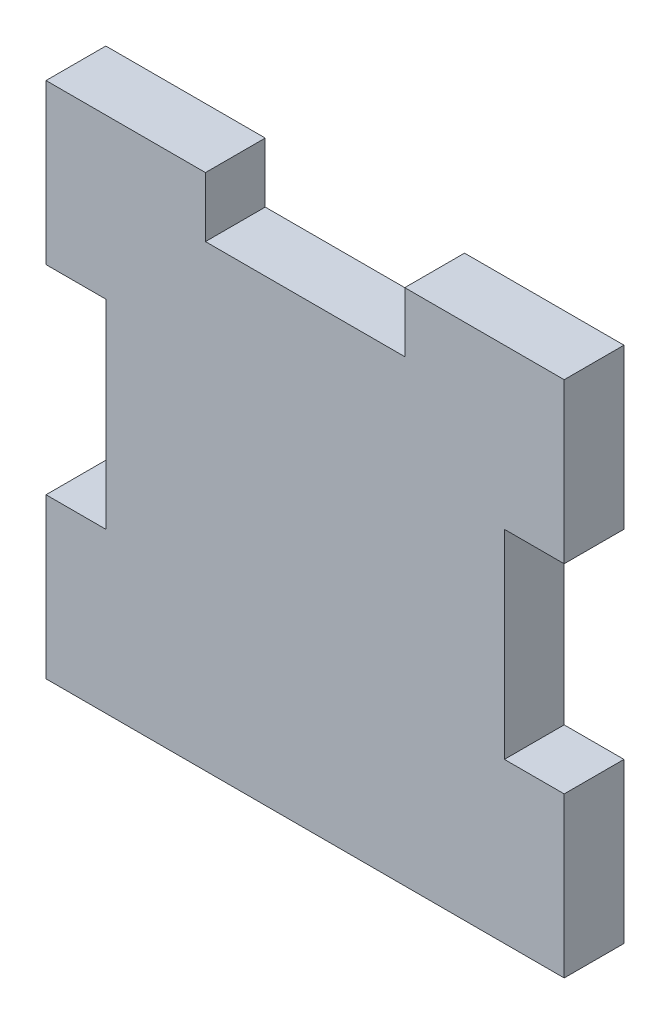
SolidWorks part; units mm, degrees
ref_plane "Front Plane" through (0, 0, 0) normal (0, 0, 1) x (1, 0, 0)
ref_plane "Top Plane" through (0, 0, 0) normal (0, 1, 0) x (1, 0, 0)
ref_plane "Right Plane" through (0, 0, 0) normal (1, 0, 0) x (0, 0, -1)
sketch "Sketch1" plane through (0, 0, 0) normal (0, 0, 1) x (1, 0, 0)
  line L0 (0, 18) -> (0, 26)
  line L1 (0, 0) -> (26, 0)
  line L2 (0, 0) -> (0, 8)
  line L3 (0, 26) -> (8, 26)
  line L4 (26, 0) -> (26, 8)
  line L6 (8, 26) -> (8, 23)
  line L7 (8, 23) -> (18, 23)
  line L8 (18, 26) -> (18, 23)
  line L9 (0, 18) -> (3, 18)
  line L11 (0, 8) -> (3, 8)
  line L12 (3, 18) -> (3, 8)
  line L13 (26, 18) -> (23, 18)
  line L15 (26, 8) -> (23, 8)
  line L16 (23, 18) -> (23, 8)
  line L17 (26, 18) -> (26, 26)
  line L18 (18, 26) -> (26, 26)
  dimension "D1" = 20
  dimension "D2" = 23
  dimension "D3" = 3
  dimension "D4" = 10
extrude "Boss-Extrude1" add sketch "Sketch1" along normal blind 3
